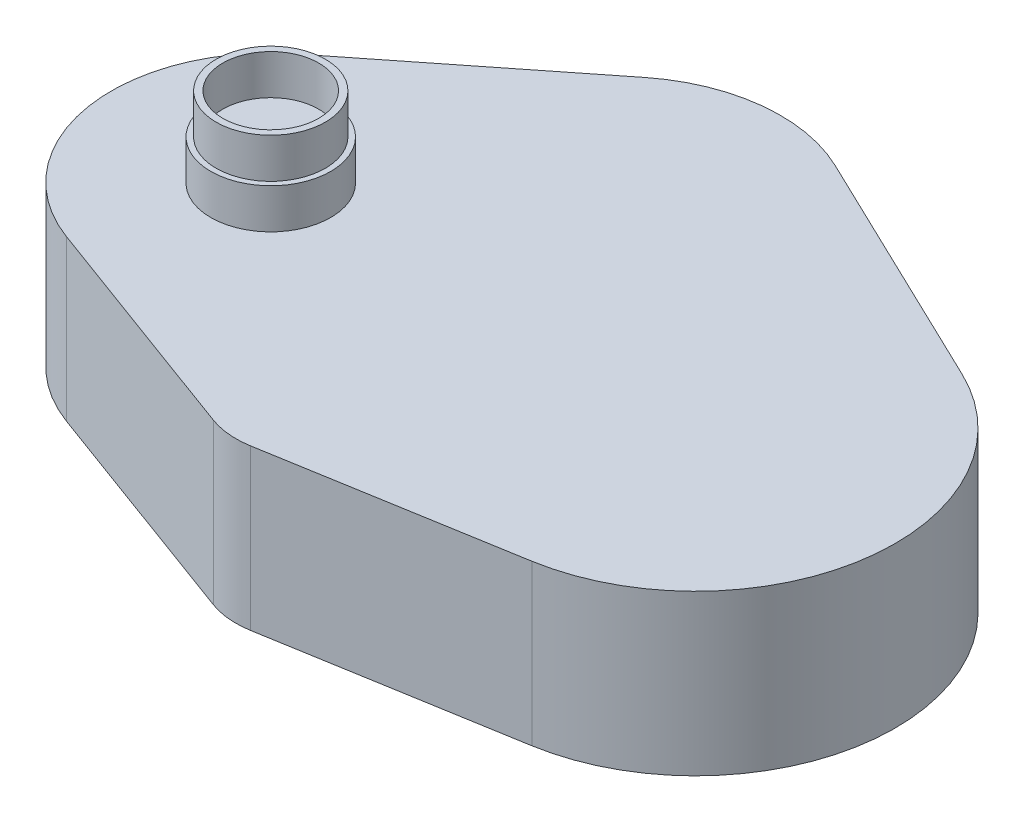
SolidWorks part; units mm, degrees
ref_plane "Front Plane" through (0, 0, 0) normal (0, 0, 1) x (1, 0, 0)
ref_plane "Top Plane" through (0, 0, 0) normal (0, 1, 0) x (1, 0, 0)
ref_plane "Right Plane" through (0, 0, 0) normal (1, 0, 0) x (0, 0, -1)
sketch "Sketch1" plane through (0, 0, 0) normal (0, 1, 0) x (1, 0, 0)
  line L0 (-31.0463, -29.2768) -> (-60.1088, -18.587)
  line L1 (-65.5601, 15.5314) -> (-41.176, 34.8234)
  line L2 (-19.7382, 37.2095) -> (10.8209, 22.5368)
  line L3 (4.1782, -24.6484) -> (-25.9229, -29.7509)
  arc A0 (4.1782, -24.6484) -> (10.8209, 22.5368) centre (0, 0) ccw
  arc A1 (-65.5601, 15.5314) -> (-60.1088, -18.587) centre (-53.2721, 0) ccw
  arc A3 (-19.7382, 37.2095) -> (-41.176, 34.8234) centre (-28.5477, 18.8619) ccw
  arc A4 (-31.0463, -29.2768) -> (-25.9229, -29.7509) centre (-27.5942, -19.8916) ccw
  dimension "D1" = 10
extrude "Boss-Extrude1" add sketch "Sketch1" along normal blind 20
sketch "Sketch2" plane through (0, 20, 0) normal (0, 1, 0) x (1, 0, 0)
  circle A0 centre (-53.1296, 0) radius 7.5
extrude "Boss-Extrude2" add sketch "Sketch2" along normal blind 5
sketch "Sketch3" plane through (0, 25, 0) normal (0, 1, 0) x (1, 0, 0)
  circle A0 centre (-53.1296, 0) radius 6
  circle A1 centre (-53.1296, 0) radius 6.8291
extrude "Boss-Extrude3" add sketch "Sketch3" along normal blind 5
